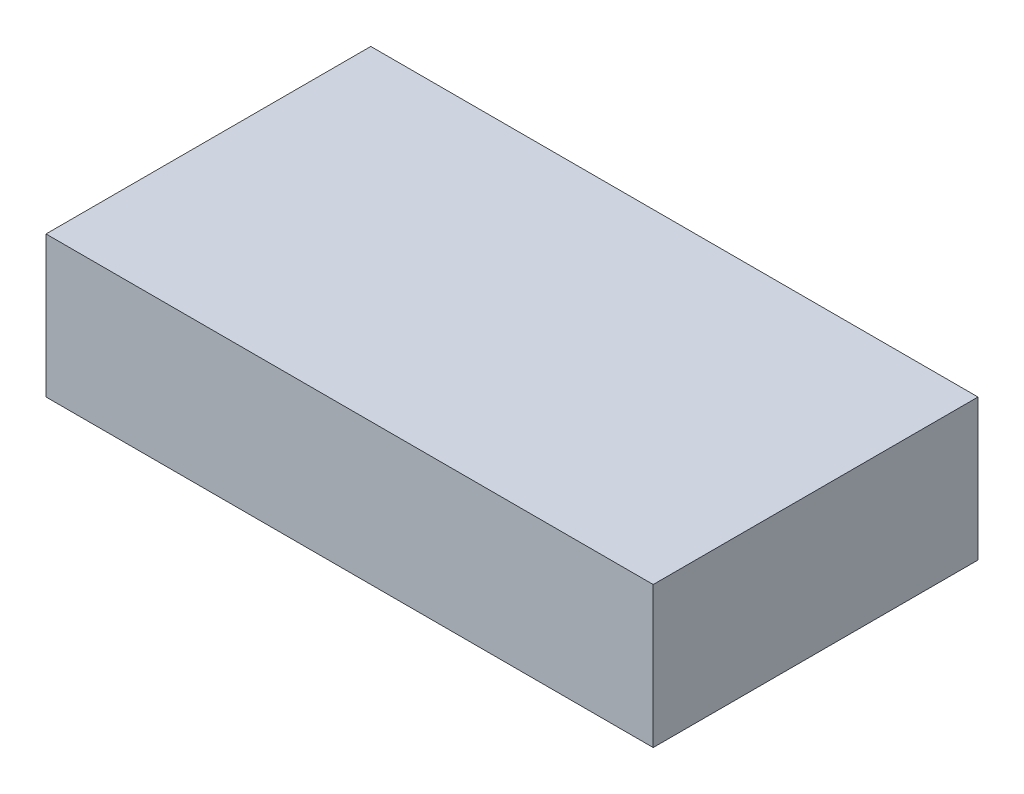
SolidWorks part; units mm, degrees
ref_plane "Front Plane" through (0, 0, 0) normal (0, 0, 1) x (1, 0, 0)
ref_plane "Top Plane" through (0, 0, 0) normal (0, 1, 0) x (1, 0, 0)
ref_plane "Right Plane" through (0, 0, 0) normal (1, 0, 0) x (0, 0, -1)
sketch "Sketch1" plane through (0, 0, 0) normal (0, 1, 0) x (1, 0, 0)
  line L1 (-107.5, -57.5) -> (107.5, -57.5)
  line L2 (-107.5, -57.5) -> (-107.5, 57.5)
  line L3 (-107.5, 57.5) -> (107.5, 57.5)
  line L4 (107.5, -57.5) -> (107.5, 57.5)
  line L5 (-107.5, -57.5) -> (107.5, 57.5) construction
  line L6 (-107.5, 57.5) -> (107.5, -57.5) construction
  point P0 (0, 0)
  dimension "D1" = 115
  dimension "D2" = 215
extrude "Boss-Extrude1" add sketch "Sketch1" along normal blind 50
